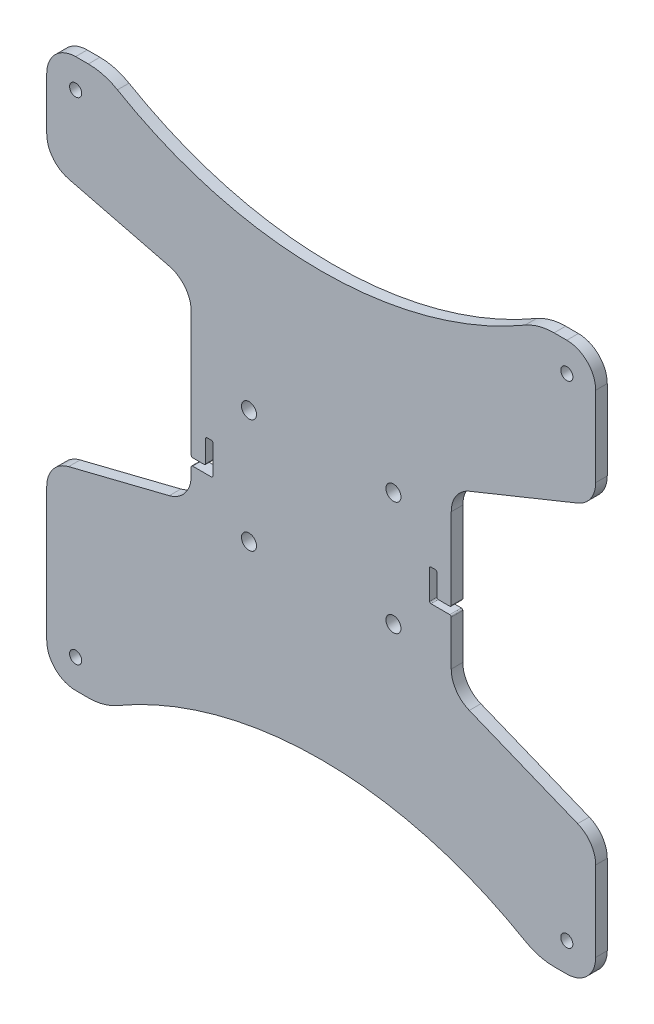
SolidWorks part; units mm, degrees
ref_plane "Front Plane" through (0, 0, 0) normal (0, 0, 1) x (1, 0, 0)
ref_plane "Top Plane" through (0, 0, 0) normal (0, 1, 0) x (1, 0, 0)
ref_plane "Right Plane" through (0, 0, 0) normal (1, 0, 0) x (0, 0, -1)
ref_plane "Plane1" through (0, 0, 0) normal (0, 0, -1) x (-1, 0, 0)
sketch "Sketch1" plane through (0, 0, 0) normal (0, 0, -1) x (-1, 0, 0)
  line L0 (87.4254, -29.1063) -> (52.5746, -20.3937)
  line L1 (45, -10.6922) -> (45, -8)
  line L2 (44.5, -7.5) -> (38, -7.5)
  line L3 (37.5, -7) -> (37.5, 3)
  line L4 (38, 3.5) -> (39.5, 3.5)
  line L5 (40, 3) -> (40, -4.5)
  line L6 (40.5, -5) -> (44.5, -5)
  line L7 (45, -4.5) -> (45, 38.6922)
  line L8 (52.5746, 48.3937) -> (87.4254, 57.1063)
  line L9 (95, 66.8078) -> (95, 85)
  line L10 (85, 95) -> (80.6, 95)
  line L11 (-80.6, 95) -> (-85, 95)
  line L12 (-95, 85) -> (-95, 57.3099)
  line L13 (-88.7544, 48.0415) -> (-51.2456, 32.8477)
  line L14 (-45, 23.5792) -> (-45, -4.5)
  line L15 (-44.5, -5) -> (-40.5, -5)
  line L16 (-40, -4.5) -> (-40, 3)
  line L17 (-39.5, 3.5) -> (-38, 3.5)
  line L18 (-37.5, 3) -> (-37.5, -7)
  line L19 (-38, -7.5) -> (-44.5, -7.5)
  line L20 (-45, -8) -> (-45, -23.5792)
  line L21 (-51.2456, -32.8477) -> (-88.7544, -48.0415)
  line L22 (-95, -57.3099) -> (-95, -85)
  line L23 (-85, -95) -> (-80.6, -95)
  line L24 (80.6, -95) -> (85, -95)
  line L25 (95, -85) -> (95, -38.8078)
  circle A0 centre (-85, -85) radius 2.1
  circle A1 centre (-85, 85) radius 2.1
  circle A2 centre (85, 85) radius 2.1
  circle A3 centre (85, -85) radius 2.1
  circle A4 centre (25, 19.0063) radius 2.6
  circle A5 centre (25, -20.3937) radius 2.6
  circle A6 centre (-25, -20.1) radius 2.6
  circle A7 centre (-25, 19.3) radius 2.6
  arc A8 (52.5746, -20.3937) -> (45, -10.6922) centre (55, -10.6922) cw
  arc A9 (45, -8) -> (44.5, -7.5) centre (44.5, -8) ccw
  arc A10 (38, -7.5) -> (37.5, -7) centre (38, -7) cw
  arc A11 (37.5, 3) -> (38, 3.5) centre (38, 3) cw
  arc A12 (39.5, 3.5) -> (40, 3) centre (39.5, 3) cw
  arc A13 (40, -4.5) -> (40.5, -5) centre (40.5, -4.5) ccw
  arc A14 (44.5, -5) -> (45, -4.5) centre (44.5, -4.5) ccw
  arc A15 (45, 38.6922) -> (52.5746, 48.3937) centre (55, 38.6922) cw
  arc A16 (87.4254, 57.1063) -> (95, 66.8078) centre (85, 66.8078) ccw
  arc A17 (95, 85) -> (85, 95) centre (85, 85) ccw
  arc A18 (80.6, 95) -> (70.525, 92.277) centre (80.6, 75) ccw
  arc A19 (70.525, 92.277) -> (-70.525, 92.277) centre (0, 213.2159) cw
  arc A20 (-70.525, 92.277) -> (-80.6, 95) centre (-80.6, 75) ccw
  arc A21 (-85, 95) -> (-95, 85) centre (-85, 85) ccw
  arc A22 (-95, 57.3099) -> (-88.7544, 48.0415) centre (-85, 57.3099) ccw
  arc A23 (-51.2456, 32.8477) -> (-45, 23.5792) centre (-55, 23.5792) cw
  arc A24 (-45, -4.5) -> (-44.5, -5) centre (-44.5, -4.5) ccw
  arc A25 (-40.5, -5) -> (-40, -4.5) centre (-40.5, -4.5) ccw
  arc A26 (-40, 3) -> (-39.5, 3.5) centre (-39.5, 3) cw
  arc A27 (-38, 3.5) -> (-37.5, 3) centre (-38, 3) cw
  arc A28 (-37.5, -7) -> (-38, -7.5) centre (-38, -7) cw
  arc A29 (-44.5, -7.5) -> (-45, -8) centre (-44.5, -8) ccw
  arc A30 (-45, -23.5792) -> (-51.2456, -32.8477) centre (-55, -23.5792) cw
  arc A31 (-88.7544, -48.0415) -> (-95, -57.3099) centre (-85, -57.3099) ccw
  arc A32 (-95, -85) -> (-85, -95) centre (-85, -85) ccw
  arc A33 (-80.6, -95) -> (-70.525, -92.277) centre (-80.6, -75) ccw
  arc A34 (-70.525, -92.277) -> (70.525, -92.277) centre (0, -213.2159) cw
  arc A35 (70.525, -92.277) -> (80.6, -95) centre (80.6, -75) ccw
  arc A36 (85, -95) -> (95, -85) centre (85, -85) ccw
  arc A37 (95, -38.8078) -> (87.4254, -29.1063) centre (85, -38.8078) ccw
  point P100 (-82.8, -95)
  dimension "D1" = 39.4
  dimension "D5" = 5.2
  dimension "D6" = 4.2
  dimension "D16" = 147.8217
  dimension "D17" = 147.8217
  dimension "D24" = 15.708
  dimension "D25" = 13.2582
  dimension "D26" = 15.708
  dimension "D27" = 13.2582
  dimension "D2" = 39.4
  dimension "D3" = 20
  dimension "D4" = 20
  dimension "D7" = 10
  dimension "D8" = 10
  dimension "D9" = 7.5
  dimension "D10" = 5
  dimension "D11" = 2.5
  dimension "D12" = 11
  dimension "D13" = 3.5
  dimension "D14" = 190
  dimension "D15" = 190
  dimension "D18" = 10
  dimension "D19" = 10
  dimension "D20" = 10
  dimension "D21" = 10
  dimension "D22" = 10
  dimension "D23" = 10
extrude "Boss-Extrude1" add sketch "Sketch1" against normal blind 4
